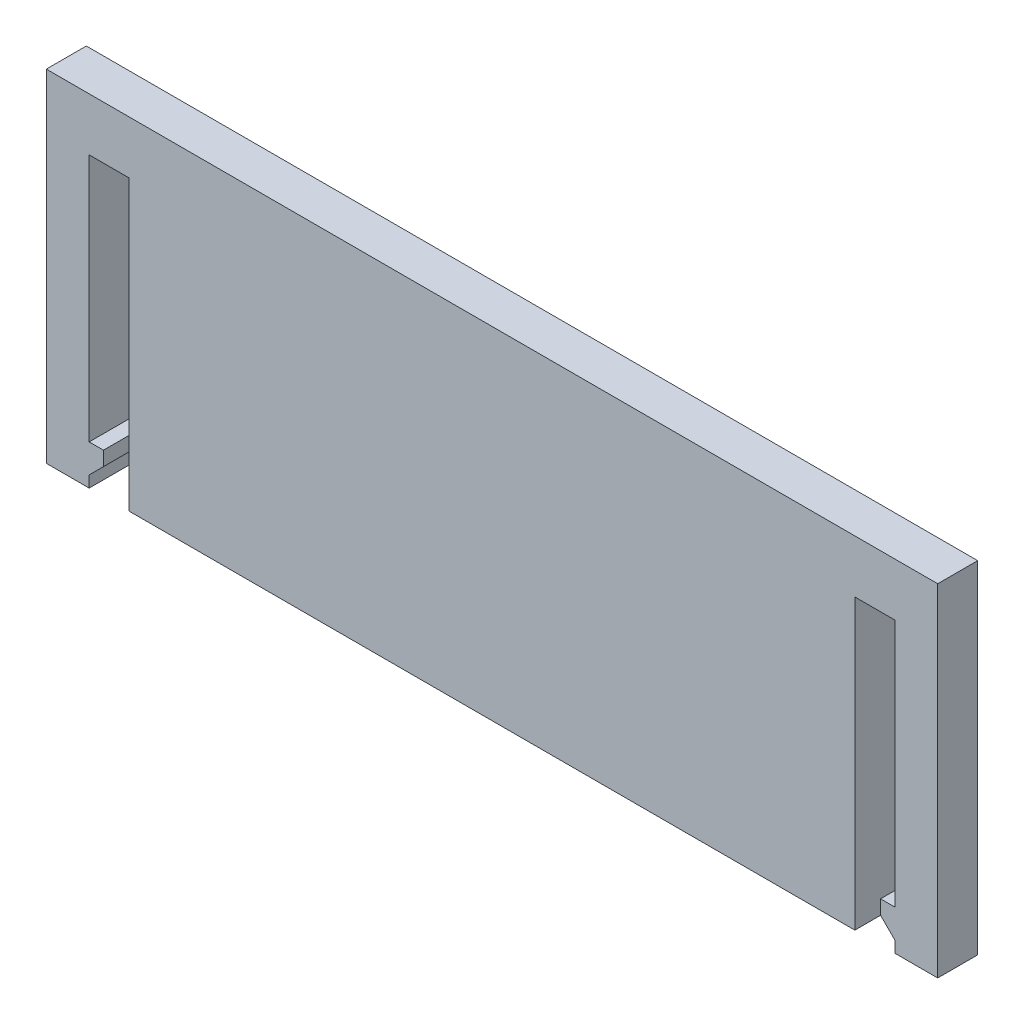
SolidWorks part; units mm, degrees
ref_plane "Front Plane" through (0, 0, 0) normal (0, 0, 1) x (1, 0, 0)
ref_plane "Top Plane" through (0, 0, 0) normal (0, 1, 0) x (1, 0, 0)
ref_plane "Right Plane" through (0, 0, 0) normal (1, 0, 0) x (0, 0, -1)
sketch "Sketch1" plane through (0, 0, 0) normal (0, 0, 1) x (1, 0, 0)
  line L0 (-50.8, -26.2997) -> (-50.8, -23.4997) construction
  line L1 (-50.8, -23.4997) -> (-53.6, -23.4997) construction
  line L2 (-53.6, -23.4997) -> (-53.6, -26.2997) construction
  line L3 (-53.6, -26.2997) -> (-50.8, -26.2997) construction
  line L4 (-50.8, -6.0975) -> (-50.8, -2.3975) construction
  line L5 (-50.8, -2.3975) -> (-53.6, -2.3975) construction
  line L6 (-53.6, -2.3975) -> (-53.6, -6.0975) construction
  line L7 (-53.6, -6.0975) -> (-50.8, -6.0975) construction
  line L8 (2.8, -26.2997) -> (2.8, -23.4997) construction
  line L9 (2.8, -23.4997) -> (0, -23.4997) construction
  line L10 (0, -23.4997) -> (0, -26.2997) construction
  line L11 (0, -26.2997) -> (2.8, -26.2997) construction
  line L12 (2.8, -6.0975) -> (2.8, -2.3975) construction
  line L13 (2.8, -2.3975) -> (0, -2.3975) construction
  line L14 (0, -2.3975) -> (0, -6.0975) construction
  line L15 (0, -6.0975) -> (2.8, -6.0975) construction
  line L16 (-50.8, -26.2997) -> (-50.8, -23.4997) construction
  line L17 (-50.8, -23.4997) -> (-53.6, -23.4997) construction
  line L18 (-53.6, -23.4997) -> (-53.6, -26.2997) construction
  line L19 (-53.6, -26.2997) -> (-50.8, -26.2997) construction
  line L20 (-50.8, -6.0975) -> (-50.8, -2.3975) construction
  line L21 (-50.8, -2.3975) -> (-53.6, -2.3975) construction
  line L22 (-53.6, -2.3975) -> (-53.6, -6.0975) construction
  line L23 (-53.6, -6.0975) -> (-50.8, -6.0975) construction
  line L24 (2.8, -26.2997) -> (2.8, -23.4997) construction
  line L25 (2.8, -23.4997) -> (0, -23.4997) construction
  line L26 (0, -23.4997) -> (0, -26.2997) construction
  line L27 (0, -26.2997) -> (2.8, -26.2997) construction
  line L28 (2.8, -6.0975) -> (2.8, -2.3975) construction
  line L29 (2.8, -2.3975) -> (0, -2.3975) construction
  line L30 (0, -2.3975) -> (0, -6.0975) construction
  line L31 (0, -6.0975) -> (2.8, -6.0975) construction
  line L33 (-56.6, -2.3975) -> (5.8, -2.3975)
  line L34 (-56.6, -2.3975) -> (-56.6, -26.2997)
  line L35 (-56.6, -26.2997) -> (5.8, -26.2997)
  line L36 (5.8, -2.3975) -> (5.8, -26.2997)
  line L37 (-56.6, -2.3975) -> (5.8, -26.2997) construction
  line L38 (-56.6, -26.2997) -> (5.8, -2.3975) construction
  line L39 (-53.6, -6.0975) -> (-50.8, -6.0975)
  line L40 (-53.6, -6.0975) -> (-53.6, -23.4997)
  line L41 (-53.6, -23.4997) -> (-50.8, -23.4997)
  line L42 (-50.8, -6.0975) -> (-50.8, -23.4997)
  line L43 (0, -6.0975) -> (2.8, -6.0975)
  line L44 (0, -6.0975) -> (0, -23.4997)
  line L45 (0, -23.4997) -> (2.8, -23.4997)
  line L46 (2.8, -6.0975) -> (2.8, -23.4997)
  point P2 (-25.4, -14.3486)
  dimension "D1" = 3
  dimension "D2" = 3
extrude "Boss-Extrude1" add sketch "Sketch1" along normal blind 2.8
sketch "Sketch2" plane through (0, 0, 2.8) normal (0, 0, 1) x (1, 0, 0)
  line L0 (-56.6, -26.2997) -> (5.8, -26.2997) construction
  line L1 (-53.6, -23.4997) -> (-50.8, -23.4997)
  line L2 (-53.6, -23.4997) -> (-53.6, -26.2997)
  line L3 (-53.6, -26.2997) -> (-50.8, -26.2997)
  line L4 (-50.8, -23.4997) -> (-50.8, -26.2997)
  line L5 (-50.8, -23.4997) -> (-50.8, -6.0975) construction
  line L6 (-53.6, -23.4997) -> (-52.6, -23.4997)
  line L7 (-52.6, -23.4997) -> (-52.6, -24.4997)
  line L8 (-52.6, -24.4997) -> (-53.6, -25.4997)
  line M11 (-56.6, -26.2997) -> (5.8, -26.2997)
  line M14 (-50.8, -23.4997) -> (-53.6, -23.4997)
  dimension "D1" = 1
  dimension "D2" = 1
  dimension "D3" = 135
extrude "Cut-Extrude1" cut sketch "Sketch2" against normal through all contours L7 L8 L2 L4 M11 M14
ref_plane "Plane1" through (-25.4, 0, 0) normal (-1, 0, 0) x (0, 0, 1)
mirror "Mirror1" about plane through (-25.4, 0, 0) normal (-1, 0, 0) of "Cut-Extrude1"
sketch "Sketch4" plane through (0, 0, 0) normal (0, 0, -1) x (-1, 0, 0)
  line L0 (-5.8, -2.3975) -> (56.6, -26.2997) construction
  line L1 (3.175, -6.0936) -> (47.625, -6.0936)
  line L2 (3.175, -6.0936) -> (3.175, -22.6036)
  line L3 (3.175, -22.6036) -> (47.625, -22.6036)
  line L4 (47.625, -6.0936) -> (47.625, -22.6036)
  line L5 (3.175, -6.0936) -> (47.625, -22.6036) construction
  line L6 (3.175, -22.6036) -> (47.625, -6.0936) construction
  point P0 (25.4, -14.3486)
  point P9 (25.4, -14.3486)
  point P10 (39.35, -6.5456)
  dimension "D1" = 44.45
  dimension "D2" = 16.51
extrude "Cut-Extrude2" cut sketch "Sketch4" against normal blind 1
sketch "Sketch5" plane through (0, 0, 1) normal (0, 0, -1) x (-1, 0, 0)
  line L0 (3.175, -6.0936) -> (3.825, -6.0936)
  line L1 (47.625, -6.0936) -> (3.175, -6.0936) construction
  line L2 (3.175, -6.0936) -> (3.175, -7.3936)
  line L3 (3.175, -6.0936) -> (3.175, -22.6036) construction
  arc A0 (3.175, -7.3936) -> (3.825, -6.0936) centre (4.8, -7.3936) cw
  dimension "D1" = 0.65
  dimension "D2" = 1.3
extrude "Boss-Extrude2" add sketch "Sketch5" along normal up to surface (1 mm away) up to face at (-25.4, -14.3486, 0)
ref_plane "Plane2" through (0, -14.3486, 0) normal (0, 1, 0) x (1, 0, 0)
mirror "Mirror2" about plane through (-25.4, 0, 0) normal (-1, 0, 0) of "Boss-Extrude2" second plane through (0, -14.3486, 0) second plane normal (0, 1, 0)
equation "\"thick\"= 2.80mm"
equation "\"D1@Boss-Extrude1\"=\"thick\""
